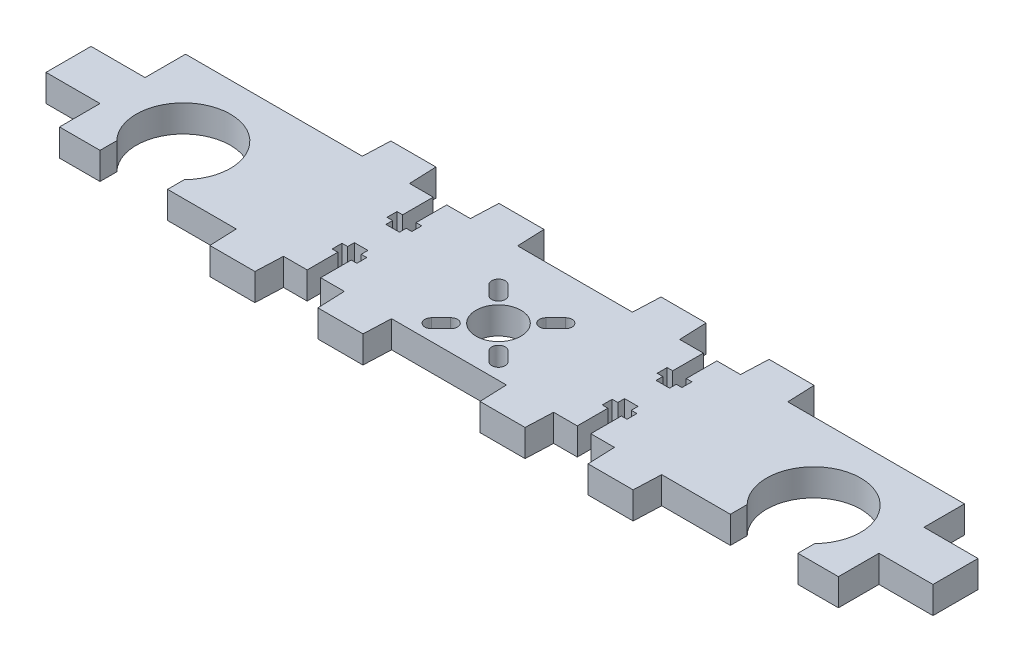
SolidWorks part; units mm, degrees
ref_plane "Спереди" through (0, 0, 0) normal (0, 0, 1) x (1, 0, 0)
ref_plane "Сверху" through (0, 0, 0) normal (0, 1, 0) x (1, 0, 0)
ref_plane "Справа" through (0, 0, 0) normal (1, 0, 0) x (0, 0, -1)
sketch "Эскиз1" plane through (0, 0, 0) normal (0, 1, 0) x (1, 0, 0)
  line L0 (-8.2217, -9.2322) -> (-6.1004, -7.1109)
  line L1 (-3.9791, -9.2322) -> (-6.1004, -11.3535)
  line L2 (-6.1004, 5.6171) -> (-3.9791, 3.4957)
  line L3 (-6.1004, 1.3744) -> (-8.2217, 3.4957)
  line L4 (8.7489, -9.2322) -> (6.6275, -7.1109)
  line L5 (4.5062, -9.2322) -> (6.6275, -11.3535)
  line L6 (6.6275, 5.6171) -> (4.5062, 3.4957)
  line L7 (6.6275, 1.3744) -> (8.7489, 3.4957)
  line L8 (86.7636, -13.8682) -> (86.7636, -4.8682)
  line L9 (77.7636, -13.8682) -> (86.7636, -13.8682)
  line L10 (77.7636, -10.1451) -> (77.7636, -13.8682)
  line L11 (62.7636, -13.8682) -> (62.7636, -10.1451)
  line L12 (47.5136, -13.8682) -> (62.7636, -13.8682)
  line L13 (47.2636, -19.9682) -> (47.5136, -13.8682)
  line L14 (37.2636, -19.9682) -> (47.2636, -19.9682)
  line L15 (37.0136, -13.8682) -> (37.2636, -19.9682)
  line L16 (31.7636, -13.8682) -> (37.0136, -13.8682)
  line L17 (31.7636, -7.0682) -> (31.7636, -13.8682)
  line L18 (33.0136, -7.0682) -> (31.7636, -7.0682)
  line L19 (33.0136, -4.8682) -> (33.0136, -7.0682)
  line L20 (31.7636, -4.8682) -> (33.0136, -4.8682)
  line L21 (31.7636, -3.3682) -> (31.7636, -4.8682)
  line L22 (28.7636, -3.3682) -> (31.7636, -3.3682)
  line L23 (28.7636, -4.8682) -> (28.7636, -3.3682)
  line L24 (27.5136, -4.8682) -> (28.7636, -4.8682)
  line L25 (27.5136, -7.0682) -> (27.5136, -4.8682)
  line L26 (28.7636, -7.0682) -> (27.5136, -7.0682)
  line L27 (28.7636, -13.8682) -> (28.7636, -7.0682)
  line L28 (23.5136, -13.8682) -> (28.7636, -13.8682)
  line L29 (23.2636, -19.9682) -> (23.5136, -13.8682)
  line L30 (13.2636, -19.9682) -> (23.2636, -19.9682)
  line L31 (13.0136, -13.8682) -> (13.2636, -19.9682)
  line L32 (-12.4864, -13.8682) -> (13.0136, -13.8682)
  line L33 (-12.4864, -13.8682) -> (-12.7364, -19.9682)
  line L34 (-12.7364, -19.9682) -> (-22.7364, -19.9682)
  line L35 (-22.7364, -19.9682) -> (-22.9864, -13.8682)
  line L36 (-22.9864, -13.8682) -> (-28.2364, -13.8682)
  line L37 (-28.2364, -13.8682) -> (-28.2364, -7.0682)
  line L38 (-28.2364, -7.0682) -> (-26.9864, -7.0682)
  line L39 (-26.9864, -7.0682) -> (-26.9864, -4.8682)
  line L40 (-26.9864, -4.8682) -> (-28.2364, -4.8682)
  line L41 (-28.2364, -4.8682) -> (-28.2364, -3.3682)
  line L42 (-28.2364, -3.3682) -> (-31.2364, -3.3682)
  line L43 (-31.2364, -3.3682) -> (-31.2364, -4.8682)
  line L44 (-31.2364, -4.8682) -> (-32.4864, -4.8682)
  line L45 (-32.4864, -4.8682) -> (-32.4864, -7.0682)
  line L46 (-32.4864, -7.0682) -> (-31.2364, -7.0682)
  line L47 (-31.2364, -7.0682) -> (-31.2364, -13.8682)
  line L48 (-31.2364, -13.8682) -> (-36.4864, -13.8682)
  line L49 (-36.4864, -13.8682) -> (-36.7364, -19.9682)
  line L50 (-36.7364, -19.9682) -> (-46.7364, -19.9682)
  line L51 (-46.7364, -19.9682) -> (-46.9864, -13.8682)
  line L52 (-46.9864, -13.8682) -> (-62.2364, -13.8682)
  line L53 (-62.2364, -13.8682) -> (-62.2364, -10.1451)
  line L54 (-77.2364, -10.1451) -> (-77.2364, -13.8682)
  line L55 (-77.2364, -13.8682) -> (-86.2364, -13.8682)
  line L56 (-86.2364, -13.8682) -> (-86.2364, -4.8682)
  line L57 (-86.2364, -4.8682) -> (-98.2364, -4.8682)
  line L58 (-98.2364, -4.8682) -> (-98.2364, 5.1318)
  line L59 (-98.2364, 5.1318) -> (-86.2364, 5.1318)
  line L60 (-86.2364, 5.1318) -> (-86.2364, 14.1318)
  line L61 (-86.2364, 14.1318) -> (-46.9864, 14.1318)
  line L62 (-46.9864, 14.1318) -> (-46.7364, 20.2318)
  line L63 (-46.7364, 20.2318) -> (-36.7364, 20.2318)
  line L64 (-36.7364, 20.2318) -> (-36.4864, 14.1318)
  line L65 (-36.4864, 14.1318) -> (-31.2364, 14.1318)
  line L66 (-31.2364, 14.1318) -> (-31.2364, 7.3318)
  line L67 (-31.2364, 7.3318) -> (-32.4864, 7.3318)
  line L68 (-32.4864, 7.3318) -> (-32.4864, 5.1318)
  line L69 (-32.4864, 5.1318) -> (-31.2364, 5.1318)
  line L70 (-31.2364, 5.1318) -> (-31.2364, 3.6318)
  line L71 (-31.2364, 3.6318) -> (-28.2364, 3.6318)
  line L72 (-28.2364, 3.6318) -> (-28.2364, 5.1318)
  line L73 (-28.2364, 5.1318) -> (-26.9864, 5.1318)
  line L74 (-26.9864, 5.1318) -> (-26.9864, 7.3318)
  line L75 (-26.9864, 7.3318) -> (-28.2364, 7.3318)
  line L76 (-28.2364, 7.3318) -> (-28.2364, 14.1318)
  line L77 (-28.2364, 14.1318) -> (-22.9864, 14.1318)
  line L78 (-22.9864, 14.1318) -> (-22.7364, 20.2318)
  line L79 (-22.7364, 20.2318) -> (-12.7364, 20.2318)
  line L80 (-12.7364, 20.2318) -> (-12.4864, 14.1318)
  line L81 (13.0136, 14.1318) -> (-12.4864, 14.1318)
  line L82 (13.2636, 20.2318) -> (13.0136, 14.1318)
  line L83 (23.2636, 20.2318) -> (13.2636, 20.2318)
  line L84 (23.5136, 14.1318) -> (23.2636, 20.2318)
  line L85 (28.7636, 14.1318) -> (23.5136, 14.1318)
  line L86 (28.7636, 7.3318) -> (28.7636, 14.1318)
  line L87 (27.5136, 7.3318) -> (28.7636, 7.3318)
  line L88 (27.5136, 5.1318) -> (27.5136, 7.3318)
  line L89 (28.7636, 5.1318) -> (27.5136, 5.1318)
  line L90 (28.7636, 3.6318) -> (28.7636, 5.1318)
  line L91 (31.7636, 3.6318) -> (28.7636, 3.6318)
  line L92 (31.7636, 5.1318) -> (31.7636, 3.6318)
  line L93 (33.0136, 5.1318) -> (31.7636, 5.1318)
  line L94 (33.0136, 7.3318) -> (33.0136, 5.1318)
  line L95 (31.7636, 7.3318) -> (33.0136, 7.3318)
  line L96 (31.7636, 14.1318) -> (31.7636, 7.3318)
  line L97 (37.0136, 14.1318) -> (31.7636, 14.1318)
  line L98 (37.2636, 20.2318) -> (37.0136, 14.1318)
  line L99 (47.2636, 20.2318) -> (37.2636, 20.2318)
  line L100 (47.5136, 14.1318) -> (47.2636, 20.2318)
  line L101 (86.7636, 14.1318) -> (47.5136, 14.1318)
  line L102 (86.7636, 5.1318) -> (86.7636, 14.1318)
  line L103 (98.7636, 5.1318) -> (86.7636, 5.1318)
  line L104 (98.7636, -4.8682) -> (98.7636, 5.1318)
  line L105 (86.7636, -4.8682) -> (98.7636, -4.8682)
  arc A0 (-3.9791, -9.2322) -> (-6.1004, -7.1109) centre (-5.0397, -8.1715) ccw
  arc A1 (-8.2217, -9.2322) -> (-6.1004, -11.3535) centre (-7.161, -10.2928) ccw
  arc A2 (-6.1004, 1.3744) -> (-3.9791, 3.4957) centre (-5.0397, 2.4351) ccw
  arc A3 (-6.1004, 5.6171) -> (-8.2217, 3.4957) centre (-7.161, 4.5564) ccw
  arc A4 (6.6275, -11.3535) -> (8.7489, -9.2322) centre (7.6882, -10.2928) ccw
  arc A5 (6.6275, -7.1109) -> (4.5062, -9.2322) centre (5.5669, -8.1715) ccw
  arc A6 (8.7489, 3.4957) -> (6.6275, 5.6171) centre (7.6882, 4.5564) ccw
  arc A7 (4.5062, 3.4957) -> (6.6275, 1.3744) centre (5.5669, 2.4351) ccw
  arc A8 (77.7636, -10.1451) -> (62.7636, -10.1451) centre (70.2636, -2.8682) ccw
  arc A9 (-62.2364, -10.1451) -> (-77.2364, -10.1451) centre (-69.7364, -2.8682) ccw
  circle A10 centre (0.2636, -2.8682) radius 5
extrude "Бобышка-Вытянуть1" add sketch "Эскиз1" along normal blind 6
